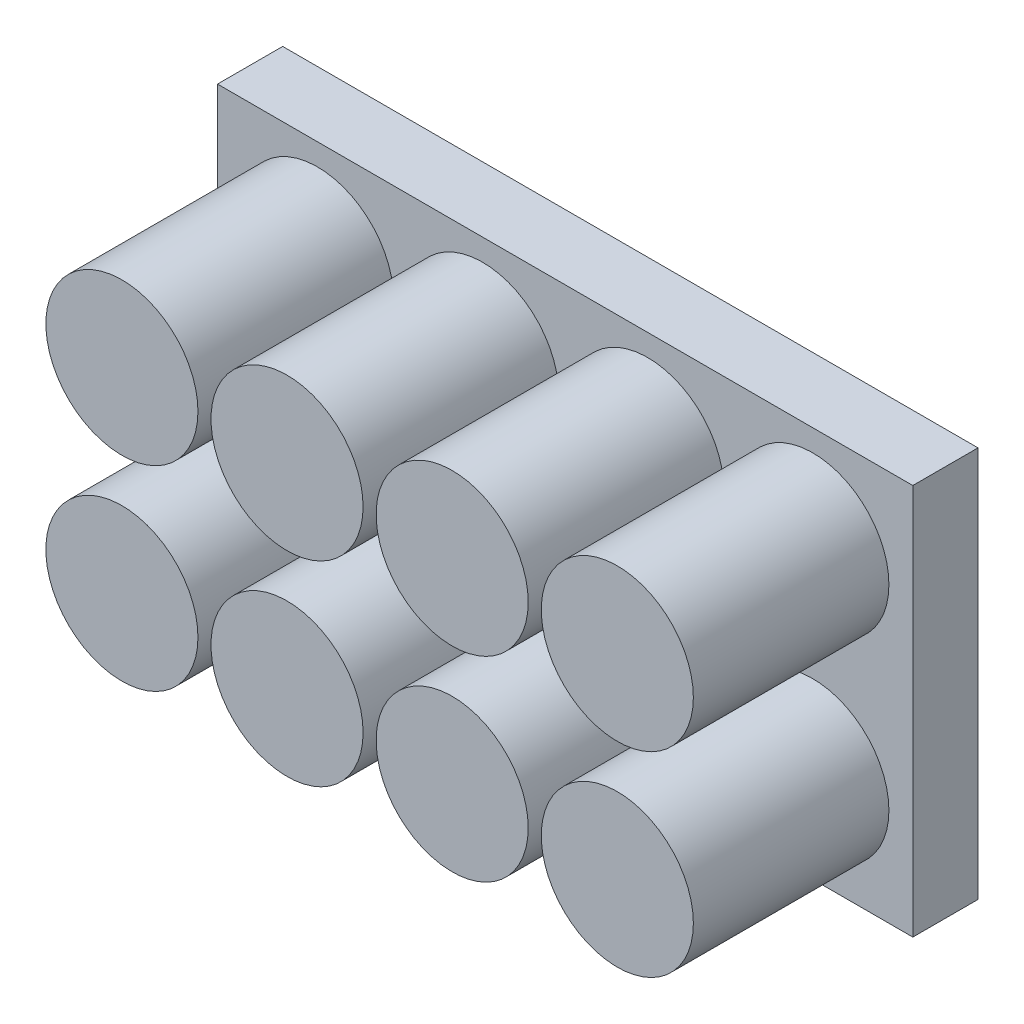
SolidWorks part; units mm, degrees
ref_plane "Plan de face" through (0, 0, 0) normal (0, 0, 1) x (1, 0, 0)
ref_plane "Plan de dessus" through (0, 0, 0) normal (0, 1, 0) x (1, 0, 0)
ref_plane "Plan de droite" through (0, 0, 0) normal (1, 0, 0) x (0, 0, -1)
sketch "Esquisse1" plane through (0, 0, 0) normal (0, 0, 1) x (1, 0, 0)
  line L1 (-75.3473, 32.7679) -> (84.6527, 32.7679)
  line L2 (-75.3473, 32.7679) -> (-75.3473, -57.2321)
  line L3 (-75.3473, -57.2321) -> (84.6527, -57.2321)
  line L4 (84.6527, 32.7679) -> (84.6527, -57.2321)
  dimension "D1" = 160
  dimension "D2" = 90
extrude "Boss.-Extru.1" add sketch "Esquisse1" along normal blind 15
sketch "Esquisse2" plane through (0, 0, 15) normal (0, 0, 1) x (1, 0, 0)
  line L0 (-75.3473, 32.7679) -> (-75.3473, -57.2321) construction
  circle A0 centre (-52.3473, 10.2679) radius 17.5
  circle A1 centre (-14.3473, 10.2679) radius 17.5
  circle A2 centre (23.6527, 10.2679) radius 17.5
  circle A3 centre (61.6527, 10.2679) radius 17.5
  circle A4 centre (-14.3473, -34.7321) radius 17.5
  circle A5 centre (23.6527, -34.7321) radius 17.5
  circle A6 centre (61.6527, -34.7321) radius 17.5
  circle A7 centre (-52.3473, -34.7321) radius 17.5
  point P6 (-75.3473, -12.2321)
  dimension "D1" = 35
  dimension "D2" = 22.5
  dimension "D5" = 23
  dimension "D3" = 4
  dimension "D4" = 2
extrude "Boss.-Extru.2" add sketch "Esquisse2" along normal blind 45
